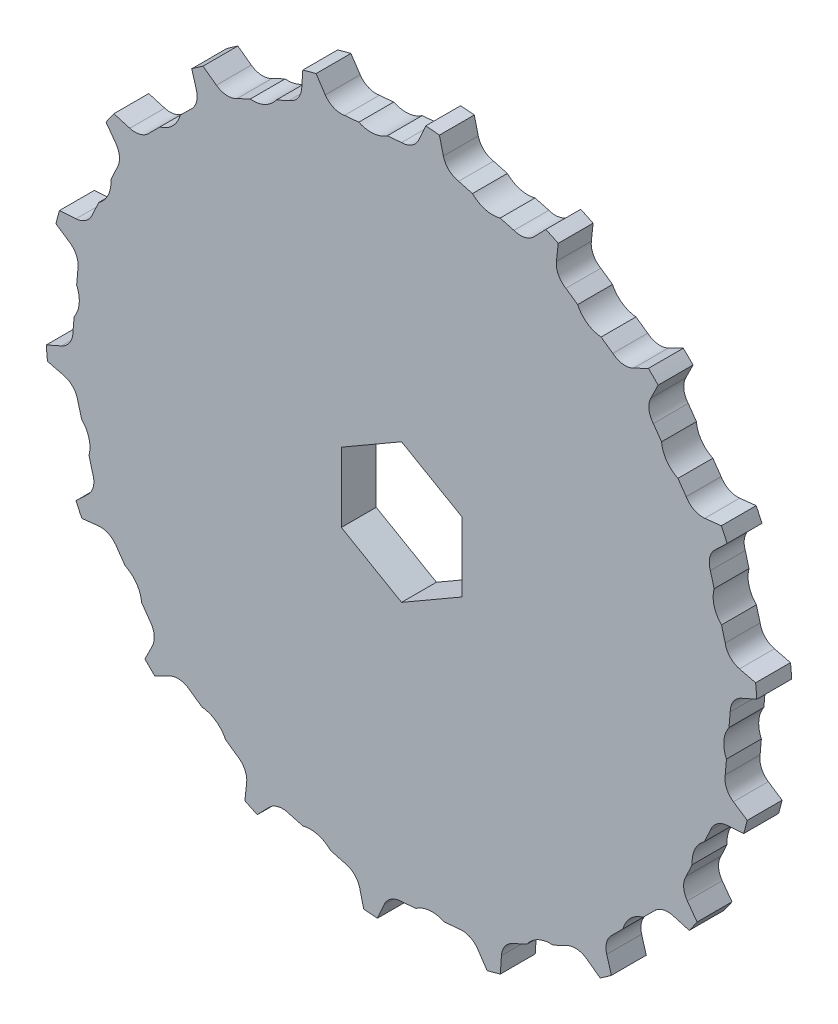
SolidWorks part; units mm, degrees
ref_plane "Front Plane" through (0, 0, 0) normal (0, 0, 1) x (1, 0, 0)
ref_plane "Top Plane" through (0, 0, 0) normal (0, 1, 0) x (1, 0, 0)
ref_plane "Right Plane" through (0, 0, 0) normal (1, 0, 0) x (0, 0, -1)
sketch "Sketch1" plane through (0, 0, 0) normal (0, 0, 1) x (1, 0, 0)
  line L0 (3.6596, 71.1503) -> (5.6741, 75.716)
  line L1 (3.6596, 71.1503) -> (8.7511, 70.7049) construction
  line L2 (7.5601, 75.551) -> (8.7511, 70.7049)
  line L3 (3.6596, 71.1503) -> (0, 0) construction
  line L4 (0, 0) -> (8.7511, 70.7049) construction
  line L5 (15.9591, 69.4339) -> (18.7358, 73.5804)
  line L6 (20.5645, 73.0904) -> (20.8959, 68.1111)
  line L7 (27.7738, 65.6078) -> (31.2283, 69.2091)
  line L8 (32.9441, 68.409) -> (32.4058, 63.4478)
  line L9 (38.7445, 59.7882) -> (42.7719, 62.7349)
  line L10 (44.3227, 61.649) -> (42.9311, 56.8567)
  line L11 (48.538, 52.1519) -> (53.0159, 54.3546)
  line L12 (54.3546, 53.0159) -> (52.1519, 48.538)
  line L13 (56.8567, 42.9311) -> (61.649, 44.3227)
  line L14 (62.7349, 42.7719) -> (59.7882, 38.7445)
  line L15 (63.4478, 32.4058) -> (68.409, 32.9441)
  line L16 (69.2091, 31.2283) -> (65.6078, 27.7738)
  line L17 (68.1111, 20.8959) -> (73.0904, 20.5645)
  line L18 (73.5804, 18.7358) -> (69.4339, 15.9591)
  line L19 (70.7049, 8.7511) -> (75.551, 7.5601)
  line L20 (75.716, 5.6741) -> (71.1503, 3.6596)
  line L21 (71.1503, -3.6596) -> (75.716, -5.6741)
  line L22 (75.551, -7.5601) -> (70.7049, -8.7511)
  line L23 (69.4339, -15.9591) -> (73.5804, -18.7358)
  line L24 (73.0904, -20.5645) -> (68.1111, -20.8959)
  line L25 (65.6078, -27.7738) -> (69.2091, -31.2283)
  line L26 (68.409, -32.9441) -> (63.4478, -32.4058)
  line L27 (59.7882, -38.7445) -> (62.7349, -42.7719)
  line L28 (61.649, -44.3227) -> (56.8567, -42.9311)
  line L29 (52.1519, -48.538) -> (54.3546, -53.0159)
  line L30 (53.0159, -54.3546) -> (48.538, -52.1519)
  line L31 (42.9311, -56.8567) -> (44.3227, -61.649)
  line L32 (42.7719, -62.7349) -> (38.7445, -59.7882)
  line L33 (32.4058, -63.4478) -> (32.9441, -68.409)
  line L34 (31.2283, -69.2091) -> (27.7738, -65.6078)
  line L35 (20.8959, -68.1111) -> (20.5645, -73.0904)
  line L36 (18.7358, -73.5804) -> (15.9591, -69.4339)
  line L37 (8.7511, -70.7049) -> (7.5601, -75.551)
  line L38 (5.6741, -75.716) -> (3.6596, -71.1503)
  line L39 (-3.6596, -71.1503) -> (-5.6741, -75.716)
  line L40 (-7.5601, -75.551) -> (-8.7511, -70.7049)
  line L41 (-15.9591, -69.4339) -> (-18.7358, -73.5804)
  line L42 (-20.5645, -73.0904) -> (-20.8959, -68.1111)
  line L43 (-27.7738, -65.6078) -> (-31.2283, -69.2091)
  line L44 (-32.9441, -68.409) -> (-32.4058, -63.4478)
  line L45 (-38.7445, -59.7882) -> (-42.7719, -62.7349)
  line L46 (-44.3227, -61.649) -> (-42.9311, -56.8567)
  line L47 (-48.538, -52.1519) -> (-53.0159, -54.3546)
  line L48 (-54.3546, -53.0159) -> (-52.1519, -48.538)
  line L49 (-56.8567, -42.9311) -> (-61.649, -44.3227)
  line L50 (-62.7349, -42.7719) -> (-59.7882, -38.7445)
  line L51 (-63.4478, -32.4058) -> (-68.409, -32.9441)
  line L52 (-69.2091, -31.2283) -> (-65.6078, -27.7738)
  line L53 (-68.1111, -20.8959) -> (-73.0904, -20.5645)
  line L54 (-73.5804, -18.7358) -> (-69.4339, -15.9591)
  line L55 (-70.7049, -8.7511) -> (-75.551, -7.5601)
  line L56 (-75.716, -5.6741) -> (-71.1503, -3.6596)
  line L57 (-71.1503, 3.6596) -> (-75.716, 5.6741)
  line L58 (-75.551, 7.5601) -> (-70.7049, 8.7511)
  line L59 (-69.4339, 15.9591) -> (-73.5804, 18.7358)
  line L60 (-73.0904, 20.5645) -> (-68.1111, 20.8959)
  line L61 (-65.6078, 27.7738) -> (-69.2091, 31.2283)
  line L62 (-68.409, 32.9441) -> (-63.4478, 32.4058)
  line L63 (-59.7882, 38.7445) -> (-62.7349, 42.7719)
  line L64 (-61.649, 44.3227) -> (-56.8567, 42.9311)
  line L65 (-52.1519, 48.538) -> (-54.3546, 53.0159)
  line L66 (-53.0159, 54.3546) -> (-48.538, 52.1519)
  line L67 (-42.9311, 56.8567) -> (-44.3227, 61.649)
  line L68 (-42.7719, 62.7349) -> (-38.7445, 59.7882)
  line L69 (-32.4058, 63.4478) -> (-32.9441, 68.409)
  line L70 (-31.2283, 69.2091) -> (-27.7738, 65.6078)
  line L71 (-20.8959, 68.1111) -> (-20.5645, 73.0904)
  line L72 (-18.7358, 73.5804) -> (-15.9591, 69.4339)
  line L73 (-8.7511, 70.7049) -> (-7.5601, 75.551)
  line L74 (-5.6741, 75.716) -> (-3.6596, 71.1503)
  line L83 (0, 72.765) -> (0, 0) construction
  line L84 (0, 0) -> (6.589, 75.3123) construction
  circle A0 centre (0, 0) radius 72.765 construction
  arc A1 (-3.9985, 72.6551) -> (3.6596, 71.1503) centre (0, 72.765) ccw
  arc A2 (4.3155, 72.6369) -> (8.3633, 72.2828) centre (0, 0) cw
  arc A3 (5.6741, 75.716) -> (7.5601, 75.551) centre (6.589, 75.3123) cw
  arc A4 (8.6787, 72.2456) -> (15.9591, 69.4339) centre (12.6355, 71.6595) ccw
  arc A5 (18.7358, 73.5804) -> (20.5645, 73.0904) centre (19.5667, 73.024) cw
  arc A6 (21.0921, 69.641) -> (27.7738, 65.6078) centre (24.8871, 68.3767) ccw
  arc A7 (31.2283, 69.2091) -> (32.9441, 68.409) centre (31.9499, 68.5169) cw
  arc A8 (32.8647, 64.9204) -> (38.7445, 59.7882) centre (36.3825, 63.0163) ccw
  arc A9 (42.7719, 62.7349) -> (44.3227, 61.649) centre (43.3624, 61.9279) cw
  arc A10 (43.6388, 58.2272) -> (48.538, 52.1519) centre (46.7724, 55.7412) ccw
  arc A11 (53.0159, 54.3546) -> (54.3546, 53.0159) centre (53.4573, 53.4573) cw
  arc A12 (53.0868, 49.7648) -> (56.8567, 42.9311) centre (55.7412, 46.7724) ccw
  arc A13 (61.649, 44.3227) -> (62.7349, 42.7719) centre (61.9279, 43.3624) cw
  arc A14 (60.9219, 39.7903) -> (63.4478, 32.4058) centre (63.0163, 36.3825) ccw
  arc A15 (68.409, 32.9441) -> (69.2091, 31.2283) centre (68.5169, 31.9499) cw
  arc A16 (66.9059, 28.6068) -> (68.1111, 20.8959) centre (68.3767, 24.8871) ccw
  arc A17 (73.0904, 20.5645) -> (73.5804, 18.7358) centre (73.024, 19.5667) cw
  arc A18 (70.8569, 16.5542) -> (70.7049, 8.7511) centre (71.6595, 12.6355) ccw
  arc A19 (75.551, 7.5601) -> (75.716, 5.6741) centre (75.3123, 6.589) cw
  arc A20 (72.6551, 3.9985) -> (71.1503, -3.6596) centre (72.765, 0) ccw
  arc A21 (75.716, -5.6741) -> (75.551, -7.5601) centre (75.3123, -6.589) cw
  arc A22 (72.2456, -8.6787) -> (69.4339, -15.9591) centre (71.6595, -12.6355) ccw
  arc A23 (73.5804, -18.7358) -> (73.0904, -20.5645) centre (73.024, -19.5667) cw
  arc A24 (69.641, -21.0921) -> (65.6078, -27.7738) centre (68.3767, -24.8871) ccw
  arc A25 (69.2091, -31.2283) -> (68.409, -32.9441) centre (68.5169, -31.9499) cw
  arc A26 (64.9204, -32.8647) -> (59.7882, -38.7445) centre (63.0163, -36.3825) ccw
  arc A27 (62.7349, -42.7719) -> (61.649, -44.3227) centre (61.9279, -43.3624) cw
  arc A28 (58.2272, -43.6388) -> (52.1519, -48.538) centre (55.7412, -46.7724) ccw
  arc A29 (54.3546, -53.0159) -> (53.0159, -54.3546) centre (53.4573, -53.4573) cw
  arc A30 (49.7648, -53.0868) -> (42.9311, -56.8567) centre (46.7724, -55.7412) ccw
  arc A31 (44.3227, -61.649) -> (42.7719, -62.7349) centre (43.3624, -61.9279) cw
  arc A32 (39.7903, -60.9219) -> (32.4058, -63.4478) centre (36.3825, -63.0163) ccw
  arc A33 (32.9441, -68.409) -> (31.2283, -69.2091) centre (31.9499, -68.5169) cw
  arc A34 (28.6068, -66.9059) -> (20.8959, -68.1111) centre (24.8871, -68.3767) ccw
  arc A35 (20.5645, -73.0904) -> (18.7358, -73.5804) centre (19.5667, -73.024) cw
  arc A36 (16.5542, -70.8569) -> (8.7511, -70.7049) centre (12.6355, -71.6595) ccw
  arc A37 (7.5601, -75.551) -> (5.6741, -75.716) centre (6.589, -75.3123) cw
  arc A38 (3.9985, -72.6551) -> (-3.6596, -71.1503) centre (0, -72.765) ccw
  arc A39 (-5.6741, -75.716) -> (-7.5601, -75.551) centre (-6.589, -75.3123) cw
  arc A40 (-8.6787, -72.2456) -> (-15.9591, -69.4339) centre (-12.6355, -71.6595) ccw
  arc A41 (-18.7358, -73.5804) -> (-20.5645, -73.0904) centre (-19.5667, -73.024) cw
  arc A42 (-21.0921, -69.641) -> (-27.7738, -65.6078) centre (-24.8871, -68.3767) ccw
  arc A43 (-31.2283, -69.2091) -> (-32.9441, -68.409) centre (-31.9499, -68.5169) cw
  arc A44 (-32.8647, -64.9204) -> (-38.7445, -59.7882) centre (-36.3825, -63.0163) ccw
  arc A45 (-42.7719, -62.7349) -> (-44.3227, -61.649) centre (-43.3624, -61.9279) cw
  arc A46 (-43.6388, -58.2272) -> (-48.538, -52.1519) centre (-46.7724, -55.7412) ccw
  arc A47 (-53.0159, -54.3546) -> (-54.3546, -53.0159) centre (-53.4573, -53.4573) cw
  arc A48 (-53.0868, -49.7648) -> (-56.8567, -42.9311) centre (-55.7412, -46.7724) ccw
  arc A49 (-61.649, -44.3227) -> (-62.7349, -42.7719) centre (-61.9279, -43.3624) cw
  arc A50 (-60.9219, -39.7903) -> (-63.4478, -32.4058) centre (-63.0163, -36.3825) ccw
  arc A51 (-68.409, -32.9441) -> (-69.2091, -31.2283) centre (-68.5169, -31.9499) cw
  arc A52 (-66.9059, -28.6068) -> (-68.1111, -20.8959) centre (-68.3767, -24.8871) ccw
  arc A53 (-73.0904, -20.5645) -> (-73.5804, -18.7358) centre (-73.024, -19.5667) cw
  arc A54 (-70.8569, -16.5542) -> (-70.7049, -8.7511) centre (-71.6595, -12.6355) ccw
  arc A55 (-75.551, -7.5601) -> (-75.716, -5.6741) centre (-75.3123, -6.589) cw
  arc A56 (-72.6551, -3.9985) -> (-71.1503, 3.6596) centre (-72.765, 0) ccw
  arc A57 (-75.716, 5.6741) -> (-75.551, 7.5601) centre (-75.3123, 6.589) cw
  arc A58 (-72.2456, 8.6787) -> (-69.4339, 15.9591) centre (-71.6595, 12.6355) ccw
  arc A59 (-73.5804, 18.7358) -> (-73.0904, 20.5645) centre (-73.024, 19.5667) cw
  arc A60 (-69.641, 21.0921) -> (-65.6078, 27.7738) centre (-68.3767, 24.8871) ccw
  arc A61 (-69.2091, 31.2283) -> (-68.409, 32.9441) centre (-68.5169, 31.9499) cw
  arc A62 (-64.9204, 32.8647) -> (-59.7882, 38.7445) centre (-63.0163, 36.3825) ccw
  arc A63 (-62.7349, 42.7719) -> (-61.649, 44.3227) centre (-61.9279, 43.3624) cw
  arc A64 (-58.2272, 43.6388) -> (-52.1519, 48.538) centre (-55.7412, 46.7724) ccw
  arc A65 (-54.3546, 53.0159) -> (-53.0159, 54.3546) centre (-53.4573, 53.4573) cw
  arc A66 (-49.7648, 53.0868) -> (-42.9311, 56.8567) centre (-46.7724, 55.7412) ccw
  arc A67 (-44.3227, 61.649) -> (-42.7719, 62.7349) centre (-43.3624, 61.9279) cw
  arc A68 (-39.7903, 60.9219) -> (-32.4058, 63.4478) centre (-36.3825, 63.0163) ccw
  arc A69 (-32.9441, 68.409) -> (-31.2283, 69.2091) centre (-31.9499, 68.5169) cw
  arc A70 (-28.6068, 66.9059) -> (-20.8959, 68.1111) centre (-24.8871, 68.3767) ccw
  arc A71 (-20.5645, 73.0904) -> (-18.7358, 73.5804) centre (-19.5667, 73.024) cw
  arc A72 (-16.5542, 70.8569) -> (-8.7511, 70.7049) centre (-12.6355, 71.6595) ccw
  arc A73 (-7.5601, 75.551) -> (-5.6741, 75.716) centre (-6.589, 75.3123) cw
  point P289 (0, 0)
  dimension "D1" = 145.53
  dimension "D2" = 4
  dimension "D5" = 1
  dimension "D6" = 75.6
  dimension "D3" = 5
  dimension "D4" = 36
extrude "Boss-Extrude1" add sketch "Sketch1" along normal blind 7.3
sketch "Sketch2" plane through (0, 0, 7.3) normal (0, 0, 1) x (1, 0, 0)
  circle A0 centre (0, 0) radius 12.5
  dimension "D1" = 25
extrude "Boss-Extrude2" add sketch "Sketch2" along normal blind 40
sketch "Sketch5" plane through (0, 0, 0) normal (0, 0, -1) x (-1, 0, 0)
  line L0 (0, 68.765) -> (2.9886, 68.5035)
  line L1 (0, 68.765) -> (0.7057, 76.8309)
  line L2 (11.9409, 67.7203) -> (12.6466, 75.7862)
  line L3 (0.7057, 76.8309) -> (12.6466, 75.7862)
  line L4 (8.9523, 67.9818) -> (11.9409, 67.7203)
  arc A0 (2.9886, 68.5035) -> (8.9523, 67.9818) centre (6.4237, 73.4229) ccw
  arc A3 (-3.6596, 71.1503) -> (3.6596, 71.1503) centre (0, 72.765) ccw construction
  arc A5 (-3.6596, 71.1503) -> (3.6596, 71.1503) centre (0, 72.765) ccw construction
  arc A7 (8.7511, 70.7049) -> (15.9591, 69.4339) centre (12.6355, 71.6595) ccw construction
  arc A8 (7.5601, 75.551) -> (5.6741, 75.716) centre (6.589, 75.3123) ccw construction
  point P19 (0, 68.765)
  point P22 (11.9409, 67.7203)
  dimension "D2" = 3
  dimension "D3" = 3
  dimension "D4" = 6
extrude "Cut-Extrude2" cut sketch "Sketch5" against normal blind 10
sketch "Sketch9" plane through (0, 0, 0) normal (0, 0, -1) x (-1, 0, 0)
  circle A0 centre (0, 0) radius 74.5
  circle A1 centre (0, 0) radius 100
  dimension "D1" = 149
  dimension "D2" = 200
extrude "Cut-Extrude5" cut sketch "Sketch9" against normal blind 10
fillet "Fillet1" radius 30 1 edges at (12.5, 0, 7.3)
sketch "Sketch3" plane through (0, 0, 47.3) normal (0, 0, 1) x (1, 0, 0)
  circle A0 centre (0, 0) radius 5
  dimension "D1" = 10
extrude "Cut-Extrude1" cut sketch "Sketch3" against normal through all
hole_wizard "Ø1.0mm Dowel Hole1" positions "3DSketch1" profile "Sketch4" hole size "Ø1.0" standard "ANSI Metric"
sketch3d "3DSketch1"
  point P0 (-6.8176, -10.4771, 42.0201)
  point P2 (-11.0684, 5.8086, 41.6583)
sketch "Sketch4" plane through (-6.8176, -10.4771, 42.0201) normal (0, 0, 1) x (0.8382, -0.5454, 0)
  line L0 (0, 0) -> (0, 34)
  line L1 (0, 34) -> (1.4, 33.1588)
  line L2 (1.4, 33.1588) -> (1.4, 0)
  line L5 (1.4, 0) -> (0, 0)
  line L10 (0, 34) -> (-1.4, 33.1588) construction
  line L11 (0, -6.35) -> (0, 107.95) construction
  dimension "Hole Dia." = 2.8
  dimension "Hole Depth" = 34
  dimension "Drill Angle" = 118
pattern_circular "CirPattern1" count 18 over 360 about axis through (0, 0, 0) along (0, 0, 1) of "Cut-Extrude2"
sketch "Sketch6" plane through (0, 0, 0) normal (0, 1, 0) x (1, 0, 0)
  line L1 (-74.3279, -7.3) -> (79.9055, -7.3)
  line L2 (-74.3279, -7.3) -> (-74.3279, -52.0573)
  line L3 (-74.3279, -52.0573) -> (79.9055, -52.0573)
  line L4 (79.9055, -7.3) -> (79.9055, -52.0573)
extrude "Cut-Extrude3" cut sketch "Sketch6" against normal through all both and the other way through all
sketch "Sketch7" plane through (0, 0, 0) normal (0, 0, -1) x (-1, 0, 0)
  line L1 (12.6, -7.2746) -> (12.6, 7.2746)
  line L2 (12.6, 7.2746) -> (0, 14.5492)
  line L3 (0, 14.5492) -> (-12.6, 7.2746)
  line L4 (-12.6, 7.2746) -> (-12.6, -7.2746)
  line L5 (-12.6, -7.2746) -> (0, -14.5492)
  line L6 (0, -14.5492) -> (12.6, -7.2746)
  circle A0 centre (0, 0) radius 12.6 construction
  dimension "D1" = 25.2
extrude "Cut-Extrude4" cut sketch "Sketch7" against normal through all both
sketch "Sketch8" plane through (0, 0, 7.3) normal (0, 0, 1) x (1, 0, 0)
  circle A0 centre (-12.6355, 71.6595) radius 12.7
  circle A1 centre (-12.6355, 71.6595) radius 8.7313
  circle A2 centre (-24.9213, 68.4425) radius 3.9687
  circle A5 centre (-24.9213, 68.4425) radius 12.7
  circle A6 centre (-34.2074, 77.1061) radius 3.9687
  dimension "D1" = 25.4
  dimension "D2" = 17.4625
  dimension "D3" = 7.9375
  dimension "D4" = 25.4
  dimension "D5" = 7.9375
equation "\"Teeth\"= 36"
equation "\"D4@Sketch1\"=\"Teeth\""
equation "\"D6@Sketch1\"=84/40*\"Teeth\""
equation "\"D1@Sketch1\"=161.70/40*\"Teeth\""
equation "\"D3@Sketch1\"=4.5/\"Teeth\"*40"
equation "\"D1@CirPattern1\"=\"Teeth\"/2"
